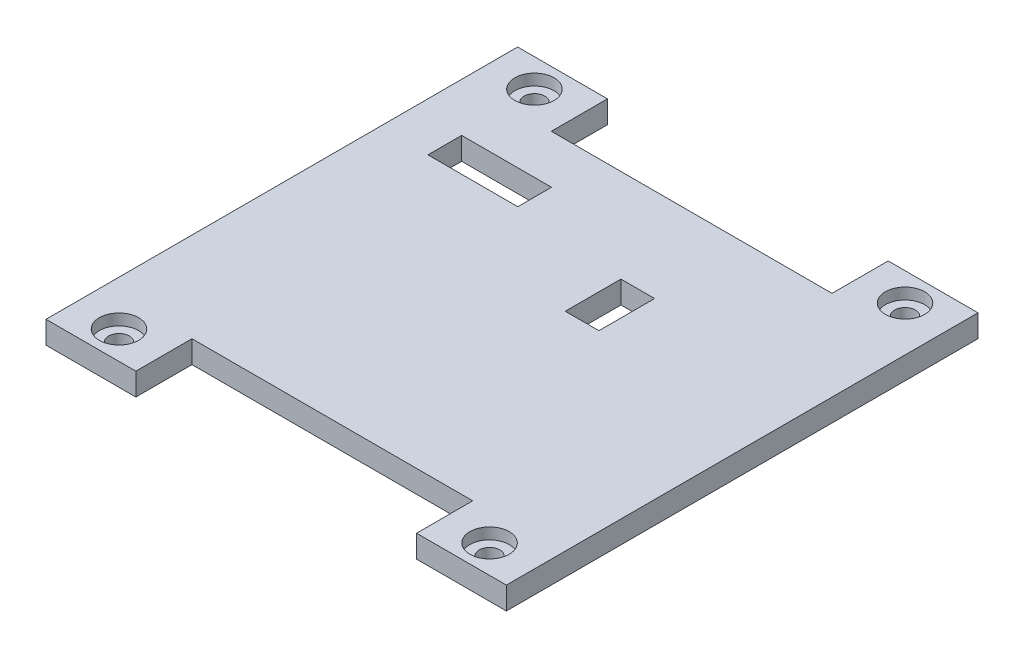
SolidWorks part; units mm, degrees
ref_plane "Спереди" through (0, 0, 0) normal (0, 0, 1) x (1, 0, 0)
ref_plane "Сверху" through (0, 0, 0) normal (0, 1, 0) x (1, 0, 0)
ref_plane "Справа" through (0, 0, 0) normal (1, 0, 0) x (0, 0, -1)
sketch "Sketch1" plane through (0, 0, 0) normal (0, 1, 0) x (1, 0, 0)
  line L1 (-13.1831, 12.3286) -> (21.8169, 12.3286)
  line L2 (-13.1831, 12.3286) -> (-13.1831, -13.6714)
  line L3 (-13.1831, -13.6714) -> (21.8169, -13.6714)
  line L4 (21.8169, 12.3286) -> (21.8169, -13.6714)
  dimension "D1" = 26
  dimension "D2" = 35
extrude "Boss-Extrude1" add sketch "Sketch1" along normal blind 2
sketch "Sketch2" plane through (0, 2, 0) normal (0, 1, 0) x (1, 0, 0)
  line L0 (21.8169, 12.3286) -> (-13.1831, 12.3286) construction
  line L1 (-16.1831, 15.3286) -> (24.8169, 15.3286)
  line L2 (-16.1831, 15.3286) -> (-16.1831, -16.6714)
  line L3 (-16.1831, -16.6714) -> (24.8169, -16.6714)
  line L4 (24.8169, 15.3286) -> (24.8169, -16.6714)
  line L5 (-13.1831, 12.3286) -> (-13.1831, -13.6714) construction
  line L6 (-13.1831, -13.6714) -> (21.8169, -13.6714) construction
  line L7 (21.8169, -13.6714) -> (21.8169, 12.3286) construction
  dimension "D1" = 3
  dimension "D2" = 3
  dimension "D3" = 3
  dimension "D4" = 3
extrude "Boss-Extrude3" add sketch "Sketch2" against normal blind 2
sketch "Sketch4" plane through (0, 0, -15.3286) normal (0, 0, -1) x (-1, 0, 0)
  line L0 (-24.8169, 0) -> (16.1831, 0) construction
  line L1 (16.1831, 2) -> (8.1831, 2)
  line L2 (16.1831, 2) -> (16.1831, 0)
  line L3 (16.1831, 0) -> (8.1831, 0)
  line L4 (8.1831, 2) -> (8.1831, 0)
  line L6 (-24.8169, 2) -> (-16.8169, 2)
  line L7 (-24.8169, 2) -> (-24.8169, 0)
  line L8 (-24.8169, 0) -> (-16.8169, 0)
  line L9 (-16.8169, 2) -> (-16.8169, 0)
  dimension "D1" = 8
  dimension "D2" = 8
extrude "Boss-Extrude4" add sketch "Sketch4" along normal blind 5
sketch "Sketch5" plane through (0, 0, 16.6714) normal (0, 0, 1) x (1, 0, 0)
  line L0 (-16.1831, 2) -> (24.8169, 2) construction
  line L1 (24.8169, 0) -> (16.8169, 0)
  line L2 (24.8169, 0) -> (24.8169, 2)
  line L3 (24.8169, 2) -> (16.8169, 2)
  line L4 (16.8169, 0) -> (16.8169, 2)
  line L6 (-16.1831, 0) -> (-8.1831, 0)
  line L7 (-16.1831, 0) -> (-16.1831, 2)
  line L8 (-16.1831, 2) -> (-8.1831, 2)
  line L9 (-8.1831, 0) -> (-8.1831, 2)
  dimension "D1" = 8
  dimension "D2" = 8
extrude "Boss-Extrude5" add sketch "Sketch5" along normal blind 5
sketch "Sketch6" plane through (0, 2, 0) normal (0, 1, 0) x (1, 0, 0)
  line L0 (-16.1831, 20.3286) -> (-8.1831, 20.3286) construction
  line L1 (16.8169, 20.3286) -> (24.8169, 20.3286) construction
  line L2 (24.8169, -21.6714) -> (16.8169, -21.6714) construction
  line L3 (-8.1831, -21.6714) -> (-16.1831, -21.6714) construction
  line L4 (-8.1831, 20.3286) -> (-8.1831, 15.3286) construction
  line L5 (24.8169, -21.6714) -> (24.8169, 20.3286) construction
  line L6 (16.8169, -21.6714) -> (16.8169, -16.6714) construction
  line L7 (-16.1831, 20.3286) -> (-16.1831, -21.6714) construction
  circle A0 centre (-12.1831, 17.8286) radius 0.925
  circle A1 centre (20.8169, 17.8286) radius 0.925
  circle A2 centre (20.8169, -19.1714) radius 0.925
  circle A3 centre (-12.1831, -19.1714) radius 0.925
  dimension "D9" = 1.85
  dimension "D1" = 2.5
  dimension "D2" = 2.5
  dimension "D3" = 2.5
  dimension "D4" = 2.5
  dimension "D5" = 4
  dimension "D6" = 4
  dimension "D7" = 4
  dimension "D8" = 4
extrude "Cut-Extrude1" cut sketch "Sketch6" against normal blind 5
sketch "Sketch7" plane through (0, 2, 0) normal (0, 1, 0) x (1, 0, 0)
  circle A0 centre (-12.1831, 17.8286) radius 1.75
  circle A1 centre (20.8169, 17.8286) radius 1.75
  circle A2 centre (20.8169, -19.1714) radius 1.75
  circle A3 centre (-12.1831, -19.1714) radius 1.75
  dimension "D1" = 3.5
extrude "Cut-Extrude2" cut sketch "Sketch7" against normal blind 1
sketch "Sketch8" plane through (0, 0, 0) normal (0, -1, 0) x (1, 0, 0)
  line L0 (24.8169, 21.6714) -> (24.8169, -20.3286) construction
  line L1 (9.3169, -7.0284) -> (12.3169, -7.0284)
  line L2 (9.3169, -7.0284) -> (9.3169, -2.0284)
  line L3 (9.3169, -2.0284) -> (12.3169, -2.0284)
  line L4 (12.3169, -7.0284) -> (12.3169, -2.0284)
  dimension "D1" = 3
  dimension "D2" = 5
  dimension "D3" = 12.5
extrude "Boss-Extrude6" add sketch "Sketch8" along normal blind 1.2
sketch "Sketch9" plane through (0, 0, 0) normal (0, -1, 0) x (1, 0, 0)
  line L1 (9.3169, -7.0284) -> (6.3169, -7.0284)
  line L2 (9.3169, -7.0284) -> (9.3169, -2.0689)
  line L3 (9.3169, -2.0689) -> (6.3169, -2.0689)
  line L4 (6.3169, -7.0284) -> (6.3169, -2.0689)
  line L5 (-11.8579, -11.0193) -> (-3.8579, -11.0193)
  line L6 (-11.8579, -11.0193) -> (-11.8579, -8.0193)
  line L7 (-11.8579, -8.0193) -> (-3.8579, -8.0193)
  line L8 (-3.8579, -11.0193) -> (-3.8579, -8.0193)
  dimension "D1" = 3
  dimension "D2" = 3
  dimension "D3" = 8
extrude "Cut-Extrude3" cut sketch "Sketch9" against normal blind 2
